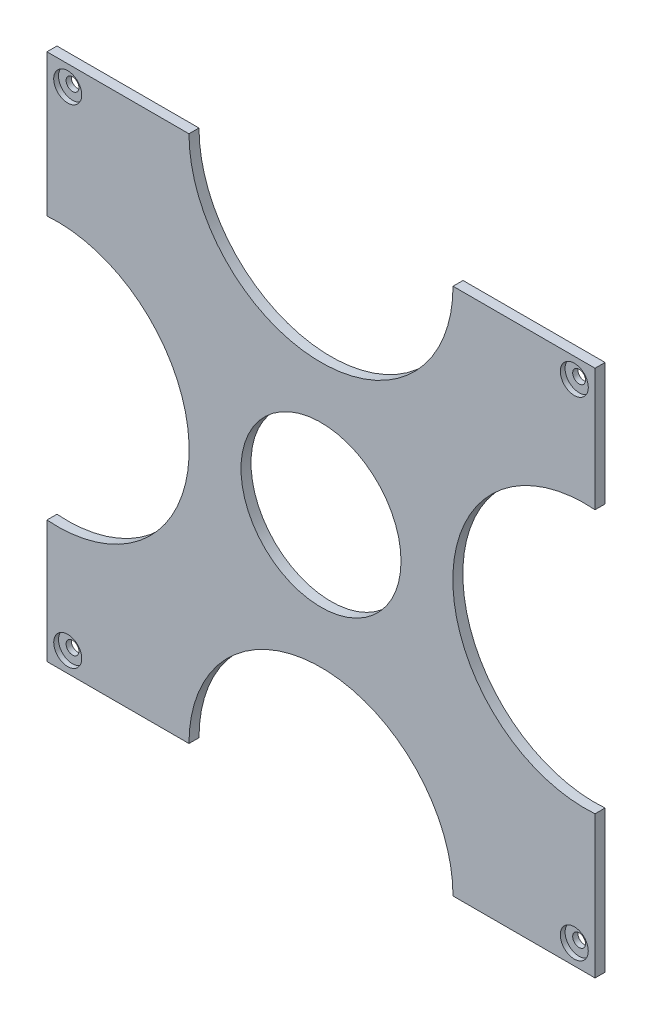
SolidWorks part; units mm, degrees
ref_plane "前视基准面" through (0, 0, 0) normal (0, 0, 1) x (1, 0, 0)
ref_plane "上视基准面" through (0, 0, 0) normal (0, 1, 0) x (1, 0, 0)
ref_plane "右视基准面" through (0, 0, 0) normal (1, 0, 0) x (0, 0, -1)
sketch "草图1" plane through (0, 0, 0) normal (0, 0, 1) x (1, 0, 0)
  line L0 (0, -55) -> (0, 55) construction
  line L1 (-68.5, 66) -> (68.5, 66)
  line L2 (-68.5, 66) -> (-68.5, -66)
  line L3 (-68.5, -66) -> (68.5, -66)
  line L4 (68.5, 66) -> (68.5, -66)
  line L5 (-68.5, 66) -> (68.5, -66) construction
  line L6 (-68.5, -66) -> (68.5, 66) construction
  line L7 (55, 0) -> (-55, 0) construction
  circle A0 centre (63.3106, -61) radius 1.6
  circle A1 centre (-63.3106, -61) radius 1.6
  circle A2 centre (-63.3106, 61) radius 1.6
  circle A3 centre (63.3106, 61) radius 1.6
  circle A4 centre (0, 66) radius 33
  circle A5 centre (0, -66) radius 33
  circle A6 centre (-65.9544, -2.4527) radius 33
  circle A7 centre (65.9544, 2.4527) radius 33
  point P0 (0, 0)
  dimension "D3" = 3.2
  dimension "D4" = 5
  dimension "D5" = 5.1894
  dimension "D6" = 66
  dimension "D1" = 137
  dimension "D2" = 132
extrude "凸台-拉伸1" add sketch "草图1" along normal blind 2.5 contours A7 L4 L1 A4 L2 A6 L3 A5 A1 A0 A2 A3
sketch "草图2" plane through (0, 0, 2.5) normal (0, 0, 1) x (1, 0, 0)
  circle A0 centre (0, 0) radius 20
extrude "切除-拉伸1" cut sketch "草图2" against normal blind 23
sketch "草图3" plane through (0, 0, 2.5) normal (0, 0, 1) x (1, 0, 0)
  line L0 (55, 0) -> (-55, 0) construction
  line L1 (0, -55) -> (0, 55) construction
  circle A0 centre (63.3106, -61) radius 3.5
  circle A1 centre (63.3106, 61) radius 3.5
  circle A2 centre (-63.3106, 61) radius 3.5
  circle A3 centre (-63.3106, -61) radius 3.5
  dimension "D1" = 7
extrude "切除-拉伸2" cut sketch "草图3" against normal blind 1.2
